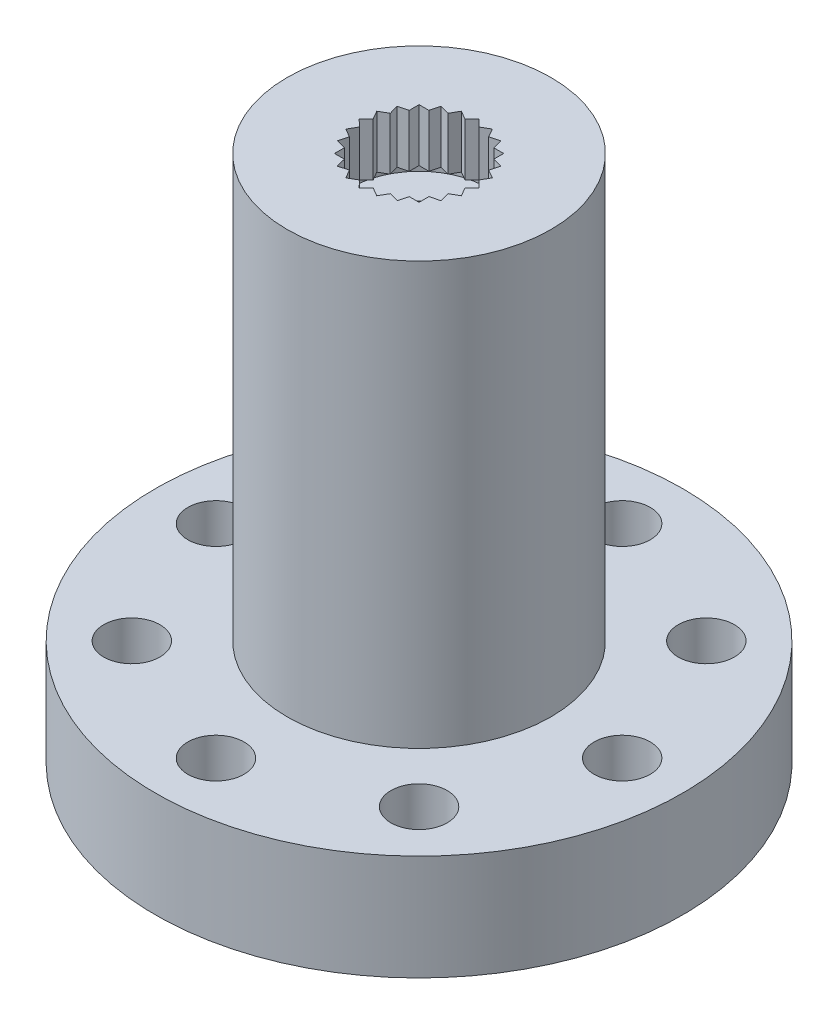
SolidWorks part; units mm, degrees
ref_plane "Front Plane" through (0, 0, 0) normal (0, 0, 1) x (1, 0, 0)
ref_plane "Top Plane" through (0, 0, 0) normal (0, 1, 0) x (1, 0, 0)
ref_plane "Right Plane" through (0, 0, 0) normal (1, 0, 0) x (0, 0, -1)
sketch "Sketch1" plane through (0, 0, 0) normal (0, 0, 1) x (1, 0, 0)
  line L0 (12.6962, 5.08) -> (0, 5.08)
  line L1 (0, 5.08) -> (0, 0)
  line L2 (0, 0) -> (12.6962, 0)
  line L3 (12.6962, 0) -> (12.6962, 5.08)
  line L4 (0, 5.08) -> (0, 0) construction
revolve "Revolve1" add sketch "Sketch1" angle 360 about L4
sketch "Sketch2" plane through (0, 5.08, 0) normal (0, 1, 0) x (-1, 0, 0)
  circle A0 centre (0, 0) radius 6.3462
extrude "Boss-Extrude1" add sketch "Sketch2" along normal blind 20.32
ref_plane "Plane1" through (0, 22.352, 0) normal (0, -1, 0) x (1, 0, 0)
sketch "Sketch3" plane through (0, 22.352, 0) normal (0, -1, 0) x (1, 0, 0)
  circle A0 centre (0, 0) radius 3.2614
extrude "Cut-Extrude1" cut sketch "Sketch3" against normal blind 0.508
sketch "Sketch4" plane through (0, 25.4, 0) normal (0, 1, 0) x (-1, 0, 0)
  line L0 (-2.4945, -1.4402) -> (-2.0353, -1.5617)
  line L1 (-2.0353, -1.5617) -> (-2.0367, -2.0367)
  line L2 (-2.0367, -2.0367) -> (-1.5617, -2.0353)
  line L3 (-1.5617, -2.0353) -> (-1.4402, -2.4945)
  line L4 (-1.4402, -2.4945) -> (-0.9817, -2.3701)
  line L5 (-0.9817, -2.3701) -> (-0.7455, -2.7822)
  line L6 (-0.7455, -2.7822) -> (-0.3349, -2.5435)
  line L7 (-0.3349, -2.5435) -> (0, -2.8804)
  line L8 (0, -2.8804) -> (0.3349, -2.5435)
  line L9 (0.3349, -2.5435) -> (0.7455, -2.7822)
  line L10 (0.7455, -2.7822) -> (0.9817, -2.3701)
  line L11 (0.9817, -2.3701) -> (1.4402, -2.4945)
  line L12 (1.4402, -2.4945) -> (1.5617, -2.0353)
  line L13 (1.5617, -2.0353) -> (2.0367, -2.0367)
  line L14 (2.0367, -2.0367) -> (2.0353, -1.5617)
  line L15 (2.0353, -1.5617) -> (2.4945, -1.4402)
  line L16 (2.4945, -1.4402) -> (2.3701, -0.9817)
  line L17 (2.3701, -0.9817) -> (2.7822, -0.7455)
  line L18 (2.7822, -0.7455) -> (2.5435, -0.3349)
  line L19 (2.5435, -0.3349) -> (2.8804, 0)
  line L20 (2.8804, 0) -> (2.5435, 0.3349)
  line L21 (2.5435, 0.3349) -> (2.7822, 0.7455)
  line L22 (2.7822, 0.7455) -> (2.3701, 0.9817)
  line L23 (2.3701, 0.9817) -> (2.4945, 1.4402)
  line L24 (2.4945, 1.4402) -> (2.0353, 1.5617)
  line L25 (2.0353, 1.5617) -> (2.0367, 2.0367)
  line L26 (2.0367, 2.0367) -> (1.5617, 2.0353)
  line L27 (1.5617, 2.0353) -> (1.4402, 2.4945)
  line L28 (1.4402, 2.4945) -> (0.9817, 2.3701)
  line L29 (0.9817, 2.3701) -> (0.7455, 2.7822)
  line L30 (0.7455, 2.7822) -> (0.3349, 2.5435)
  line L31 (0.3349, 2.5435) -> (0, 2.8804)
  line L32 (0, 2.8804) -> (-0.3349, 2.5435)
  line L33 (-0.3349, 2.5435) -> (-0.7455, 2.7822)
  line L34 (-0.7455, 2.7822) -> (-0.9817, 2.3701)
  line L35 (-0.9817, 2.3701) -> (-1.4402, 2.4945)
  line L36 (-1.4402, 2.4945) -> (-1.5617, 2.0353)
  line L37 (-1.5617, 2.0353) -> (-2.0367, 2.0367)
  line L38 (-2.0367, 2.0367) -> (-2.0353, 1.5617)
  line L39 (-2.0353, 1.5617) -> (-2.4945, 1.4402)
  line L40 (-2.4945, 1.4402) -> (-2.3701, 0.9817)
  line L41 (-2.3701, 0.9817) -> (-2.7822, 0.7455)
  line L42 (-2.7822, 0.7455) -> (-2.5435, 0.3349)
  line L43 (-2.5435, 0.3349) -> (-2.8804, 0)
  line L44 (-2.8804, 0) -> (-2.5435, -0.3349)
  line L45 (-2.5435, -0.3349) -> (-2.7822, -0.7455)
  line L46 (-2.7822, -0.7455) -> (-2.3701, -0.9817)
  line L47 (-2.3701, -0.9817) -> (-2.4945, -1.4402)
extrude "Cut-Extrude2" cut sketch "Sketch4" against normal up to next
sketch "Sketch5" plane through (0, 0, 0) normal (0, -1, 0) x (1, 0, 0)
  circle A0 centre (0, 0) radius 3.81
extrude "Cut-Extrude3" cut sketch "Sketch5" against normal blind 21.082
sketch "Sketch6" plane through (0, 21.082, 0) normal (0, -1, 0) x (1, 0, 0)
  circle A0 centre (0, 0) radius 1.5
extrude "Cut-Extrude4" cut sketch "Sketch6" against normal through all
hole_wizard "M2.5 Clearance Hole1" positions "Sketch8" profile "Sketch7" hole size "M2.5" standard "ANSI Metric"
sketch "Sketch8" plane through (0, 5.08, 0) normal (0, 1, 0) x (1, 0, 0)
  point P0 (6.9148, -6.9148)
  point P1 (0, -9.779)
  point P2 (-6.9148, -6.9148)
  point P3 (-9.779, 0)
  point P4 (-6.9148, 6.9148)
  point P5 (0, 9.779)
  point P6 (6.9148, 6.9148)
  point P7 (9.779, 0)
sketch "Sketch7" plane through (6.9148, 5.08, 6.9148) normal (1, 0, 0) x (0, 0, 1)
  line L0 (0, 0) -> (0, 5.08)
  line L1 (0, 5.08) -> (1.3525, 5.08)
  line L2 (1.3525, 5.08) -> (1.3525, 0)
  line L5 (1.3525, 0) -> (0, 0)
  line L11 (0, -6.35) -> (0, 107.95) construction
  dimension "Thru Hole Dia." = 2.7051
  dimension "Thru Hole Depth" = 5.08
sketch "Sketch9" plane through (0, 0, 0) normal (0, -1, 0) x (1, 0, 0)
  point P1 (0, 0)
  point P2 (-6.9148, 6.9148)
  dimension "D1" = 9.779
  dimension "D2" = 19.558
